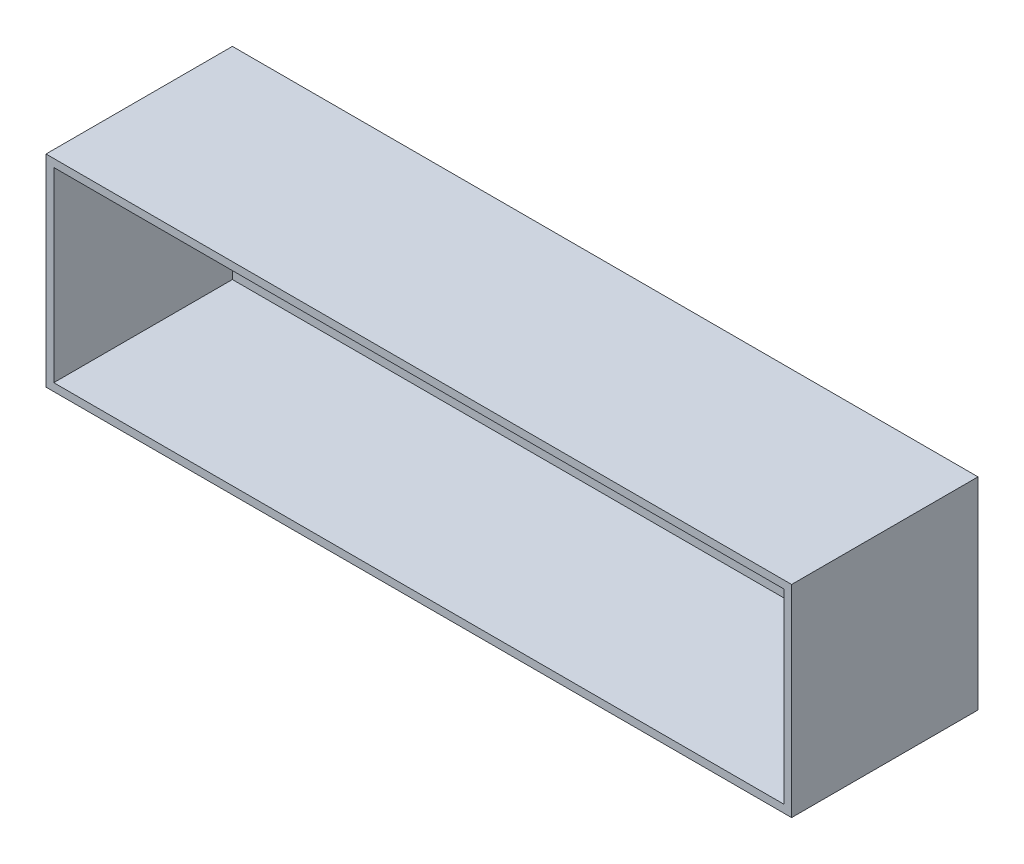
SolidWorks part; units mm, degrees
ref_plane "Front Plane" through (0, 0, 0) normal (0, 0, 1) x (1, 0, 0)
ref_plane "Top Plane" through (0, 0, 0) normal (0, 1, 0) x (1, 0, 0)
ref_plane "Right Plane" through (0, 0, 0) normal (1, 0, 0) x (0, 0, -1)
sketch "Sketch1" plane through (0, 0, 0) normal (0, 0, 1) x (1, 0, 0)
  line L0 (-304.8, 0) -> (304.8, 0)
  line L1 (-304.8, 0) -> (-304.8, 165.1)
  line L2 (-304.8, 165.1) -> (304.8, 165.1)
  line L3 (304.8, 165.1) -> (304.8, 0)
  point P4 (0, 0)
  dimension "D1" = 609.6
  dimension "D2" = 165.1
extrude "Boss-Extrude1" add sketch "Sketch1" against normal blind 152.4
sketch "Sketch2" plane through (0, 0, 0) normal (0, 0, 1) x (1, 0, 0)
  line L0 (-304.8, 82.55) -> (304.8, 82.55) construction
  line L1 (-304.8, 165.1) -> (-304.8, 0) construction
  line L2 (304.8, 0) -> (304.8, 165.1) construction
shell "Shell1" thickness 6.35
sketch "Sketch4" plane through (0, 0, -152.4) normal (0, 0, -1) x (-1, 0, 0)
  line L0 (304.8, 82.55) -> (-304.8, 82.55) construction
  line L1 (-298.45, 6.35) -> (-184.15, 6.35)
  line L2 (-298.45, 6.35) -> (-298.45, 82.55)
  line L3 (-298.45, 82.55) -> (-184.15, 82.55)
  line L4 (-184.15, 6.35) -> (-184.15, 82.55)
  dimension "D1" = 114.3
extrude "Cut-Extrude1" cut sketch "Sketch4" against normal up to surface (6.35 mm away) up to face at (0, 82.55, -146.05)
